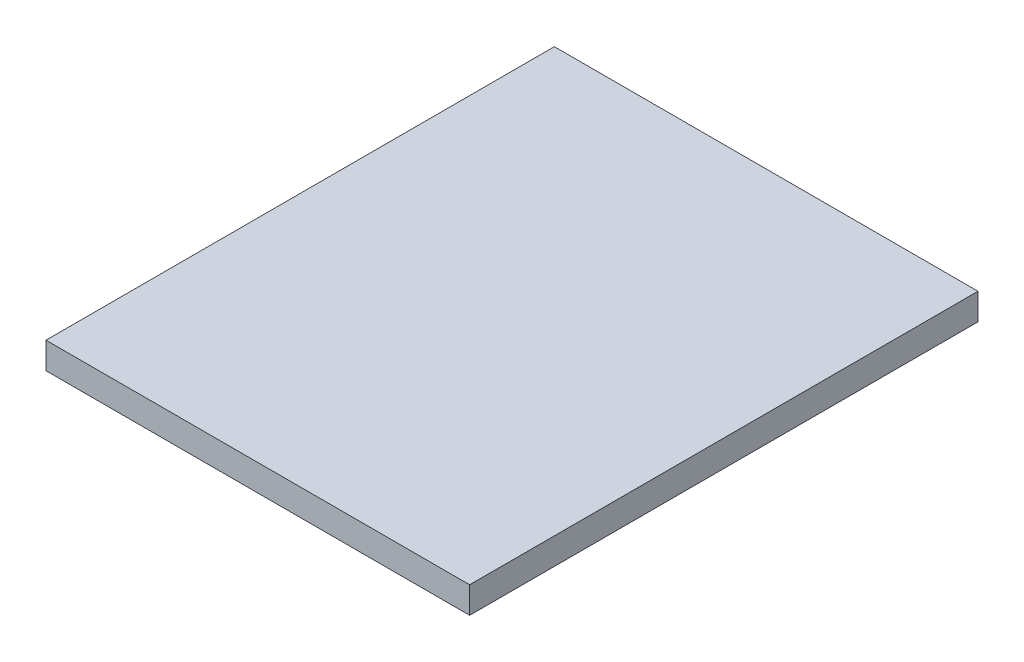
SolidWorks part; units mm, degrees
ref_plane "Front Plane" through (0, 0, 0) normal (0, 0, 1) x (1, 0, 0)
ref_plane "Top Plane" through (0, 0, 0) normal (0, 1, 0) x (1, 0, 0)
ref_plane "Right Plane" through (0, 0, 0) normal (1, 0, 0) x (0, 0, -1)
sketch "Sketch1" plane through (0, 0, 0) normal (0, 1, 0) x (1, 0, 0)
  line L1 (-47.2248, 34.5899) -> (3.5752, 34.5899)
  line L2 (-47.2248, 34.5899) -> (-47.2248, -26.3701)
  line L3 (-47.2248, -26.3701) -> (3.5752, -26.3701)
  line L4 (3.5752, 34.5899) -> (3.5752, -26.3701)
  dimension "D1" = 60.96
  dimension "D2" = 50.8
extrude "Boss-Extrude1" add sketch "Sketch1" along normal blind 3.175
